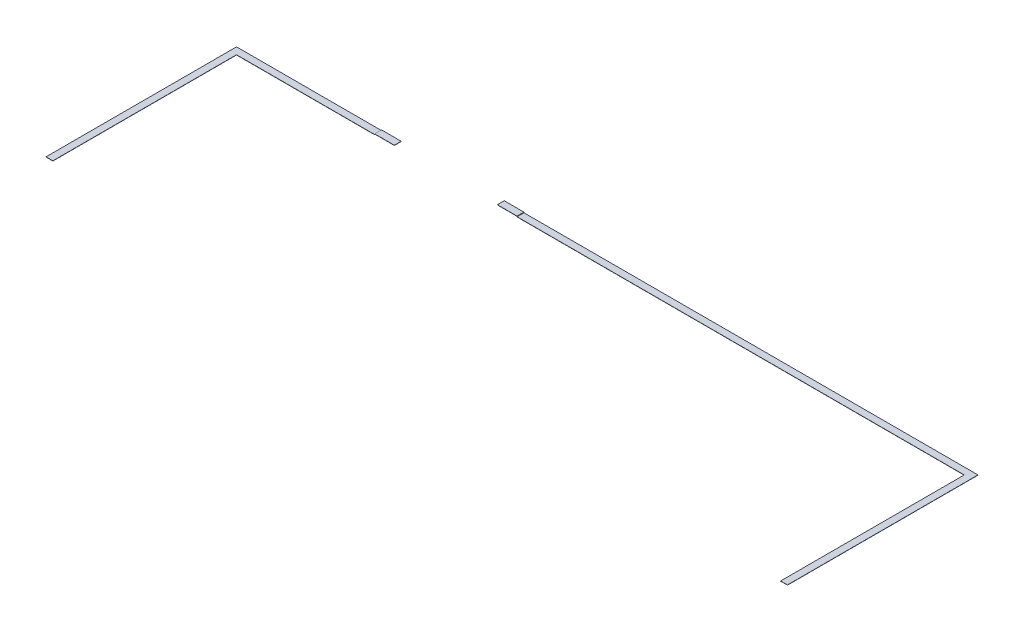
SolidWorks part; units mm, degrees
ref_plane "Front Plane" through (0, 0, 0) normal (0, 0, 1) x (1, 0, 0)
ref_plane "Top Plane" through (0, 0, 0) normal (0, 1, 0) x (1, 0, 0)
ref_plane "Right Plane" through (0, 0, 0) normal (1, 0, 0) x (0, 0, -1)
sketch "Sketch1" plane through (0, 0, 0) normal (0, 1, 0) x (1, 0, 0)
  line L0 (0, 0) -> (0, 1409.7)
  line L1 (0, 1409.7) -> (5486.4, 1409.7)
  line L2 (5486.4, 1409.7) -> (5486.4, 0)
  line L3 (50.8, 0) -> (50.8, 1358.9)
  line L4 (50.8, 1358.9) -> (5435.6, 1358.9)
  line L5 (5435.6, 1358.9) -> (5435.6, 0)
  line L6 (50.8, 0) -> (50.8, 1358.9) construction
  line L7 (5435.6, 1358.9) -> (5435.6, 0) construction
  line L8 (50.8, 0) -> (0, 0)
  line L9 (5435.6, 0) -> (5486.4, 0)
  dimension "D2" = 1409.7
  dimension "D3" = 5486.4
  dimension "D1" = 50.8
extrude "Boss-Extrude1" add sketch "Sketch1" along normal blind 1.5875
sketch "Sketch2" plane through (0, 1.5875, 0) normal (0, 1, 0) x (1, 0, 0)
  line L0 (5486.4, 1409.7) -> (0, 1409.7) construction
  line L1 (1072.6166, 1409.7) -> (2126.7166, 1409.7)
  line L2 (1072.6166, 1409.7) -> (1072.6166, 1358.9)
  line L3 (1072.6166, 1358.9) -> (2126.7166, 1358.9)
  line L4 (2126.7166, 1409.7) -> (2126.7166, 1358.9)
  line L5 (50.8, 1358.9) -> (5435.6, 1358.9) construction
  line L6 (0, 1409.7) -> (0, 0) construction
  line L7 (5486.4, 0) -> (5486.4, 1409.7) construction
  dimension "D1" = 1072.6166
  dimension "D2" = 3359.6834
extrude "Cut-Extrude1" cut sketch "Sketch2" against normal through all both and the other way through all
ref_plane "Plane1" through (0, 4.2418, 0) normal (0, -1, 0) x (-1, 0, 0)
sketch "Sketch3" plane through (0, 4.2418, 0) normal (0, -1, 0) x (-1, 0, 0)
  line L0 (-2126.7166, 1358.9) -> (-5435.6, 1358.9) construction
  line L1 (-1072.6166, 1409.7) -> (-1218.6666, 1409.7)
  line L2 (-1072.6166, 1409.7) -> (-1072.6166, 1358.9)
  line L3 (-1072.6166, 1358.9) -> (-1218.6666, 1358.9)
  line L4 (-1218.6666, 1409.7) -> (-1218.6666, 1358.9)
  line L5 (-2126.7166, 1409.7) -> (-1980.6666, 1409.7)
  line L6 (-2126.7166, 1409.7) -> (-2126.7166, 1358.9)
  line L7 (-2126.7166, 1358.9) -> (-1980.6666, 1358.9)
  line L8 (-1980.6666, 1409.7) -> (-1980.6666, 1358.9)
  dimension "D1" = 146.05
extrude "Boss-Extrude2" add sketch "Sketch3" against normal blind 1.5875 separate body
